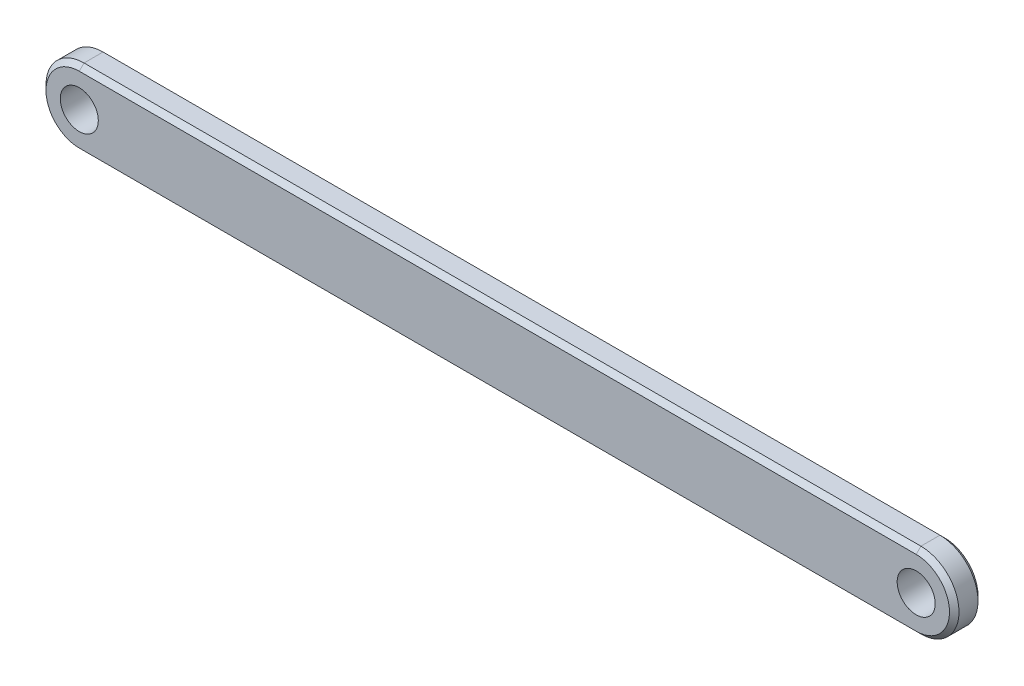
SolidWorks part; units mm, degrees
ref_plane "Front Plane" through (0, 0, 0) normal (0, 0, 1) x (1, 0, 0)
ref_plane "Top Plane" through (0, 0, 0) normal (0, 1, 0) x (1, 0, 0)
ref_plane "Right Plane" through (0, 0, 0) normal (1, 0, 0) x (0, 0, -1)
sketch "Sketch1" plane through (0, 0, 0) normal (0, 0, 1) x (1, 0, 0)
  line L0 (39.7091, 0) -> (-48.2909, 0) construction
  line L1 (39.7091, -4) -> (-48.2909, -4)
  line L2 (39.7091, 4) -> (-48.2909, 4)
  arc A0 (39.7091, -4) -> (39.7091, 4) centre (39.7091, 0) ccw
  arc A1 (-48.2909, 4) -> (-48.2909, -4) centre (-48.2909, 0) ccw
  circle A2 centre (-48.2909, 0) radius 2
  circle A3 centre (39.7091, 0) radius 2
  point P3 (-4.2909, 0)
  dimension "D3" = 4
  dimension "D4" = 4
  dimension "D1" = 88
  dimension "D2" = 8
extrude "Boss-Extrude1" add sketch "Sketch1" along normal mid plane 3
chamfer "Chamfer1" distance 0.5 angle 45 8 edges at (-52.2909, 0, -1.5) (-4.2909, -4, -1.5) (-4.2909, 4, -1.5) (43.7091, 0, -1.5) (-52.2909, 0, 1.5) (-4.2909, -4, 1.5) (-4.2909, 4, 1.5) (43.7091, 0, 1.5)
